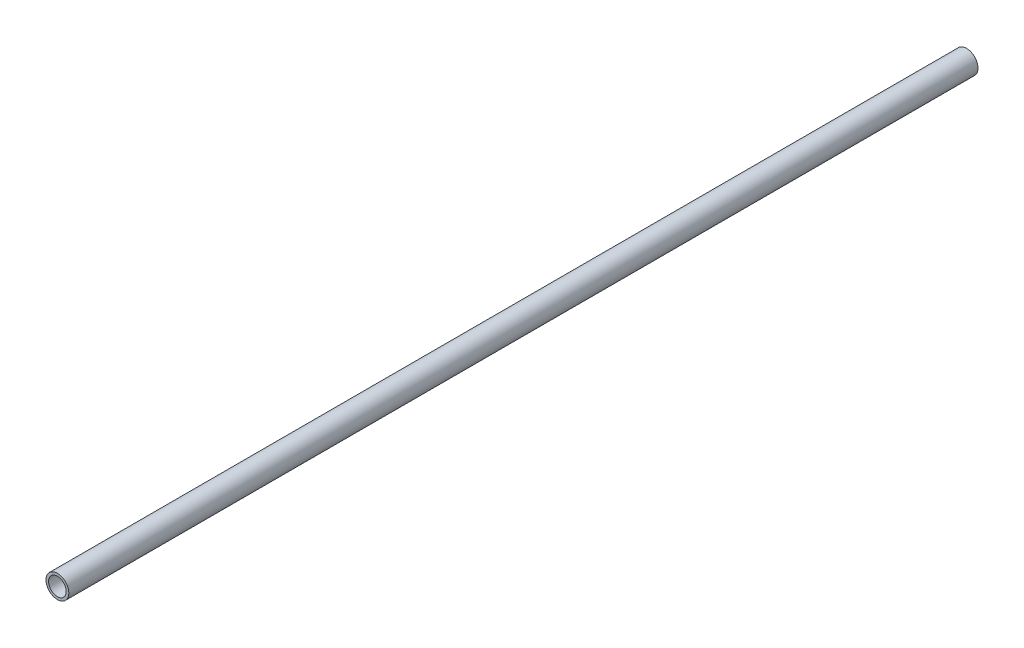
SolidWorks part; units mm, degrees
ref_plane "Front" through (0, 0, 0) normal (0, 0, 1) x (1, 0, 0)
ref_plane "Top" through (0, 0, 0) normal (0, 1, 0) x (1, 0, 0)
ref_plane "Right" through (0, 0, 0) normal (1, 0, 0) x (0, 0, -1)
sketch "Sketch1" plane through (0, 0, 0) normal (0, 0, 1) x (1, 0, 0)
  circle A0 centre (0, 0) radius 16.891
  circle A1 centre (0, 0) radius 13.081
  dimension "D1" = 33.782
  dimension "D2" = 3.81
extrude "Boss-Extrude1" add sketch "Sketch1" along normal blind 1346.2
